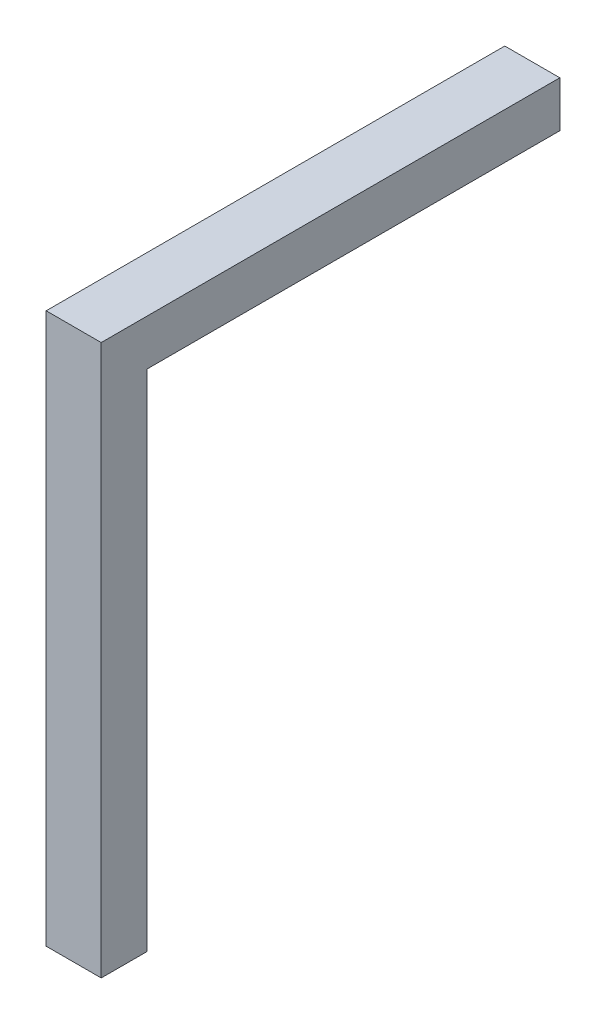
SolidWorks part; units mm, degrees
ref_plane "Front Plane" through (0, 0, 0) normal (0, 0, 1) x (1, 0, 0)
ref_plane "Top Plane" through (0, 0, 0) normal (0, 1, 0) x (1, 0, 0)
ref_plane "Right Plane" through (0, 0, 0) normal (1, 0, 0) x (0, 0, -1)
sketch "Sketch1" plane through (0, 0, 0) normal (1, 0, 0) x (0, 0, -1)
  line L0 (-10, 36.4322) -> (-60, 36.4322)
  line L1 (-60, 36.4322) -> (-60, -23.5678)
  line L2 (-60, -23.5678) -> (-55, -23.5678)
  line L3 (-55, -23.5678) -> (-55, 31.4322)
  line L4 (-55, 31.4322) -> (-10, 31.4322)
  line L5 (-10, 31.4322) -> (-10, 36.4322)
  dimension "D1" = 50
  dimension "D2" = 60
  dimension "D3" = 5
  dimension "D4" = 5
extrude "Boss-Extrude1" add sketch "Sketch1" along normal blind 6
